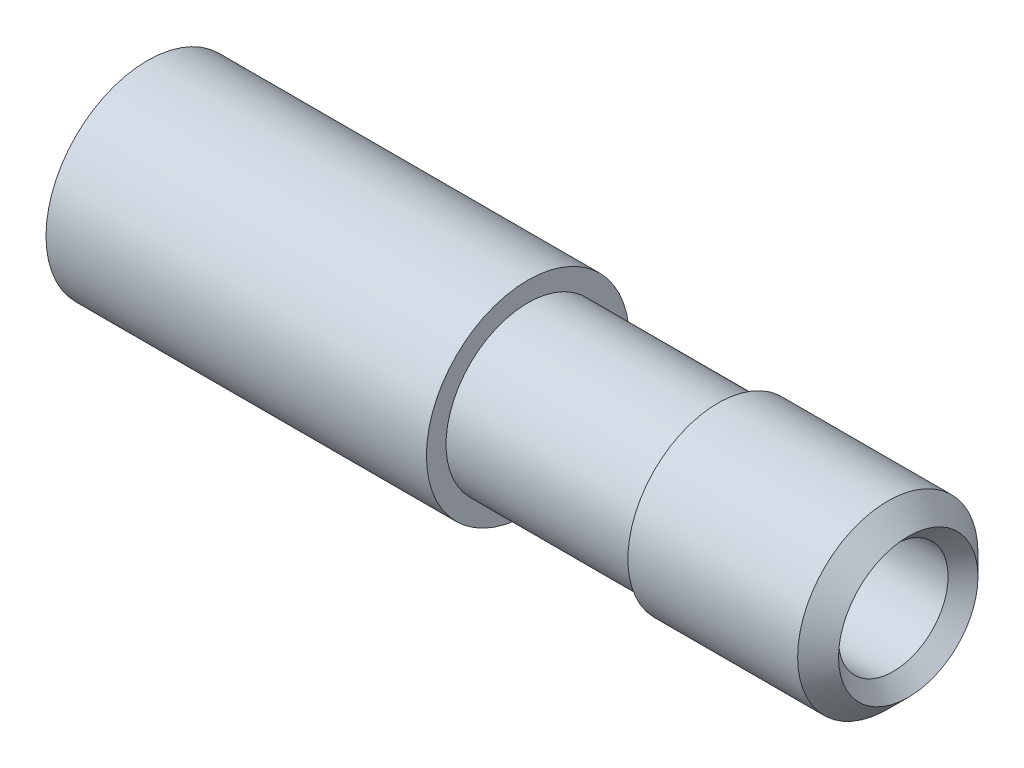
SolidWorks part; units mm, degrees
ref_plane "Front Plane" through (0, 0, 0) normal (0, 0, 1) x (1, 0, 0)
ref_plane "Top Plane" through (0, 0, 0) normal (0, 1, 0) x (1, 0, 0)
ref_plane "Right Plane" through (0, 0, 0) normal (1, 0, 0) x (0, 0, -1)
sketch "Sketch1" plane through (0, 0, 0) normal (1, 0, 0) x (0, 0, -1)
  circle A0 centre (0, 0) radius 2.5
  circle A1 centre (0, 0) radius 3.1
  circle A2 centre (0, 0) radius 4
  dimension "D1" = 5
  dimension "D2" = 6.2
  dimension "D3" = 8
extrude "Boss-Extrude2" add sketch "Sketch1" along normal blind 30 contours A2
sketch "Sketch3" plane through (0, 0, 0) normal (-1, 0, 0) x (0, 0, 1)
  circle A0 centre (0, 0) radius 2.5
  dimension "D1" = 5
extrude "Cut-Extrude1" cut sketch "Sketch3" against normal blind 12
sketch "Sketch4" plane through (30, 0, 0) normal (1, 0, 0) x (0, 0, -1)
  circle A0 centre (0, 0) radius 2.16
  dimension "D1" = 4.32
extrude "Cut-Extrude2" cut sketch "Sketch4" against normal through all
sketch "Sketch10" plane through (30, 0, 0) normal (1, 0, 0) x (0, 0, -1)
  circle A0 centre (0, 0) radius 3.556
  dimension "D1" = 7.112
extrude "Cut-Extrude3" cut sketch "Sketch10" against normal blind 15 flip side to cut
sketch "Sketch18" plane through (15, 0, 0) normal (1, 0, 0) x (0, 0, -1)
  circle A0 centre (0, 0) radius 3.2256
  dimension "D1" = 6.4511
extrude "Cut-Extrude4" cut sketch "Sketch18" along normal blind 7.5 flip side to cut
thread "9/32-40 threads" pitch 0.635 start angle 0, offset 0, length 8, pitch 0.635, diameter 7.112
ref_plane "Plane3" through (30, 0, 3.556) normal (0, -1, 0) x (0, 0, 1)
sketch "Thread Profile3" plane through (30, 0, 3.556) normal (0, -1, 0) x (0, 0, 1)
  line L0 (0, 0) -> (0, 0.635) construction
  line L11 (0, 0) -> (0, 0.5556)
  line L12 (0, 0.5556) -> (-0.3437, 0.3572)
  line L13 (-0.3437, 0.3572) -> (-0.3437, 0.1984)
  line L15 (-0.3437, 0.1984) -> (0, 0)
  line L17 (-0.3437, 0.2778) -> (0, 0.2778) construction
  point P2 (0, 0)
  dimension "Pitch" = 0.635
  dimension "Profile_Angle" = 60
  dimension "Profile_Land" = 0.1588
  dimension "Profile_Height" = 0.3437
ref_axis "Axis1" through (12, 0, 0) along (1, 0, 0)
sketch "Sketch17" plane through (0, 0, 0) normal (0, 0, 1) x (1, 0, 0)
  line L0 (28.8407, 3.9093) -> (30, 2.75)
  line L1 (30, -3.556) -> (30, 3.556) construction
  line L3 (31.3514, 3.9093) -> (28.8407, 3.9093)
  line L4 (12, 0) -> (30, 0) construction
  line L5 (30, 2.75) -> (28.8407, 1.5907)
  line L6 (28.8407, 1.5907) -> (31.3514, 1.5907)
  line L8 (31.3514, 3.9093) -> (31.3514, 1.5907)
  line L9 (28.8407, 3.9093) -> (28.8407, 1.5907) construction
  dimension "D1" = 2.75
  dimension "D2" = 45
revolve "Cut-Revolve1" cut sketch "Sketch17" angle 360 about axis through (12, 0, 0) along (1, 0, 0)
